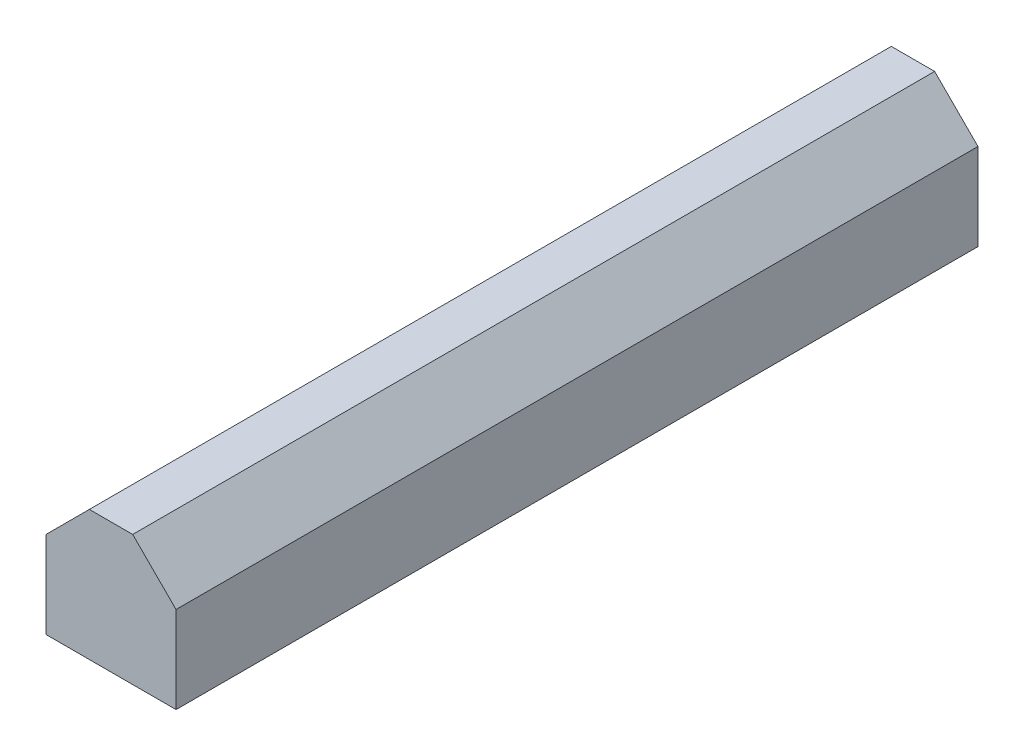
SolidWorks part; units mm, degrees
material "AISI 1020"
ref_plane "Спереди" through (0, 0, 0) normal (0, 0, 1) x (1, 0, 0)
ref_plane "Сверху" through (0, 0, 0) normal (0, 1, 0) x (1, 0, 0)
ref_plane "Справа" through (0, 0, 0) normal (1, 0, 0) x (0, 0, -1)
sketch "Эскиз1" plane through (0, 0, 0) normal (0, 0, 1) x (1, 0, 0)
  line L0 (-3, 10.583) -> (-3, 6.8739) construction
  line L1 (3, 4.5) -> (-3, 4.5)
  line L2 (3, 4.5) -> (3, 8.5)
  line L3 (1, 10.5) -> (-1, 10.5)
  line L4 (-3, 4.5) -> (-3, 8.5)
  line L5 (3, 8.5) -> (1, 10.5)
  line L6 (-1, 10.5) -> (-3, 8.5)
  line L7 (-1, 10.5) -> (-1, 4.5) construction
  point P1 (-3, 10.5)
  point P2 (3, 10.5)
extrude "Бобышка-Вытянуть1" add sketch "Эскиз1" against normal up to surface (37 mm away)
